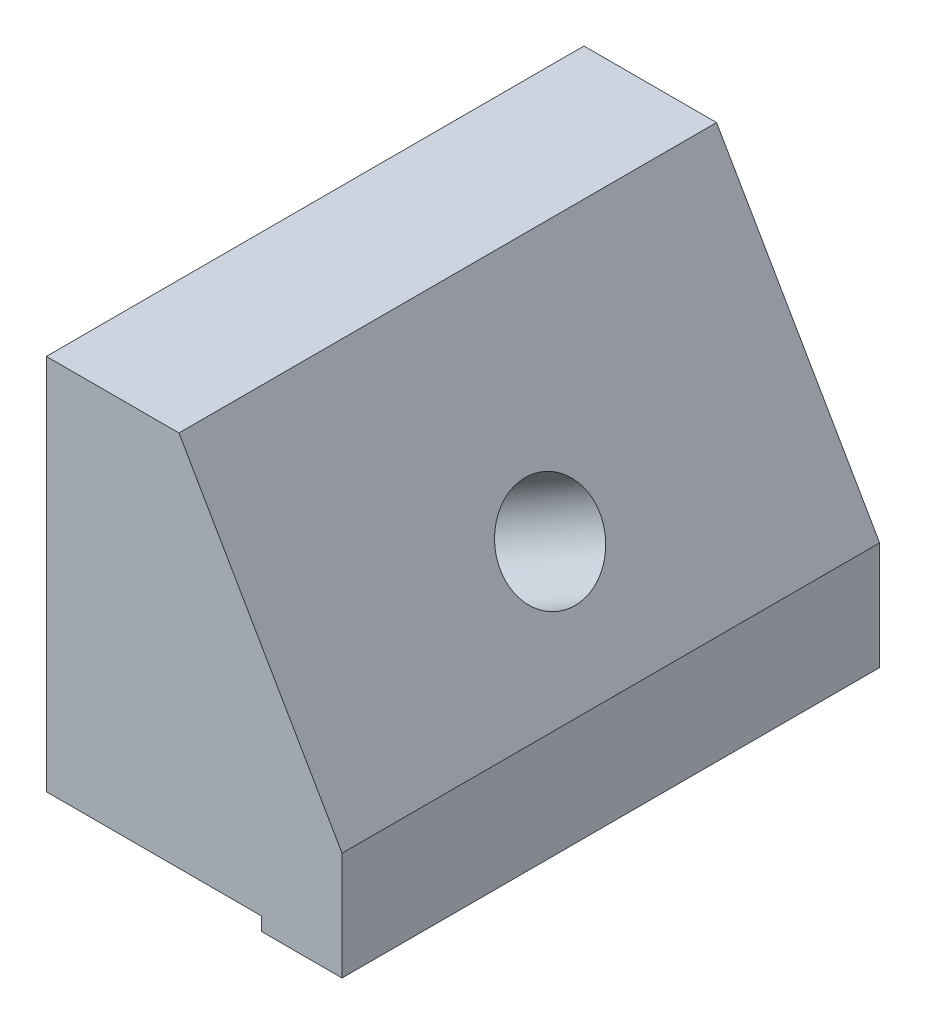
SolidWorks part; units mm, degrees
ref_plane "Спереди" through (0, 0, 0) normal (0, 0, 1) x (1, 0, 0)
ref_plane "Сверху" through (0, 0, 0) normal (0, 1, 0) x (1, 0, 0)
ref_plane "Справа" through (0, 0, 0) normal (1, 0, 0) x (0, 0, -1)
sketch "Эскиз1" plane through (0, 0, 0) normal (0, 0, 1) x (1, 0, 0)
  line L0 (-12.5, 21.6506) -> (0, 0)
  line L1 (0, 0) -> (12.9904, 7.5)
  line L2 (12.9904, 7.5) -> (0.4904, 29.1506)
  line L3 (0.4904, 29.1506) -> (-12.5, 21.6506)
extrude "Бобышка-Вытянуть1" add sketch "Эскиз1" along normal blind 20
sketch "Эскиз2" plane through (12.9904, 7.5, 0) normal (0.866, 0.5, 0) x (0, 0, -1)
  circle A0 centre (-10, 8) radius 1.85
extrude "Вырез-Вытянуть1" cut sketch "Эскиз2" against normal blind 6
sketch "Эскиз3" plane through (7.7942, 4.5, 0) normal (0.866, 0.5, 0) x (0, 0, -1)
  circle A0 centre (-10, 8) radius 1.125
extrude "Вырез-Вытянуть2" cut sketch "Эскиз3" against normal through all
sketch "Эскиз4" plane through (0, 0, 20) normal (0, 0, 1) x (1, 0, 0)
  line L0 (-12.5, 21.6506) -> (0, 0) construction
  line L1 (-3.75, 6.4952) -> (11.25, 6.4952)
  line L2 (-3.75, 6.4952) -> (-3.75, 26.7024)
  line L4 (11.25, 6.4952) -> (11.25, 10.5144)
  line L5 (0, 0) -> (12.9904, 7.5) construction
  line L6 (12.9904, 7.5) -> (0.4904, 29.1506) construction
  line L7 (0.4904, 29.1506) -> (-12.5, 21.6506) construction
  line L8 (-3.75, 26.7024) -> (1.9038, 26.7024)
  line L9 (1.9038, 26.7024) -> (11.25, 10.5144)
  point P6 (15.1592, 13.7435)
  point P7 (0, 0)
  point P10 (10.5535, 11.7208)
extrude "Вырез-Вытянуть3" cut sketch "Эскиз4" against normal through all flip side to cut
sketch "Эскиз5" plane through (0, 0, 20) normal (0, 0, 1) x (1, 0, 0)
  line L0 (1.9038, 26.7024) -> (-3.75, 26.7024) construction
  line L1 (0.25, 26.7024) -> (-3.75, 26.7024)
  line L2 (0.25, 26.7024) -> (0.25, 11.7024)
  line L3 (0.25, 11.7024) -> (-3.75, 11.7024)
  line L4 (-3.75, 26.7024) -> (-3.75, 11.7024)
  line L5 (-3.75, 26.7024) -> (-3.75, 6.4952) construction
  line L6 (-3.75, 6.4952) -> (11.25, 6.4952) construction
  line L7 (-3.75, 7.3952) -> (0.25, 7.3952)
  line L8 (-3.75, 7.3952) -> (-3.75, 6.4952)
  line L9 (-3.75, 6.4952) -> (0.25, 6.4952)
  line L10 (0.25, 7.3952) -> (0.25, 6.4952)
extrude "Вырез-Вытянуть4" cut sketch "Эскиз5" against normal through all
sketch "Эскиз6" plane through (0, 11.7024, 0) normal (0, 1, 0) x (1, 0, 0)
  line L5 (-3.75, 0) -> (-3.75, -20) construction
  line L11 (-3.75, -13) -> (0.25, -13)
  line L12 (-3.75, -13) -> (-3.75, -20)
  line L13 (-3.75, -20) -> (0.25, -20)
  line L14 (0.25, -13) -> (0.25, -20)
  line L15 (-3.75, -10) -> (11.25, -10) construction
  line L16 (11.25, 0) -> (11.25, -20) construction
  line L17 (0.25, -7) -> (0.25, 0)
  line L18 (-3.75, 0) -> (0.25, 0)
  line L19 (-3.75, -7) -> (-3.75, 0)
  line L20 (-3.75, -7) -> (0.25, -7)
extrude "Вырез-Вытянуть5" cut sketch "Эскиз6" against normal through all
sketch "Эскиз7" plane through (0, 0, 20) normal (0, 0, 1) x (1, 0, 0)
  line L0 (0.25, 21.0225) -> (5.1832, 21.0225)
  line L1 (0.25, 6.4952) -> (8.25, 6.4952)
  line L2 (0.25, 6.4952) -> (0.25, 6.9952)
  line L3 (0.25, 6.9952) -> (8.25, 6.9952)
  line L4 (8.25, 6.4952) -> (8.25, 6.9952)
  line L5 (0.25, 6.4952) -> (0.25, 26.7024) construction
  line L6 (11.25, 10.5144) -> (1.9038, 26.7024) construction
  line L8 (0.25, 26.7024) -> (0.25, 21.0225)
  line L9 (1.9038, 26.7024) -> (0.25, 26.7024) construction
  line L10 (0.25, 26.7024) -> (1.9038, 26.7024)
  line L11 (1.9038, 26.7024) -> (5.1832, 21.0225)
extrude "Вырез-Вытянуть6" cut sketch "Эскиз7" against normal through all
sketch "Эскиз8" plane through (0, 6.9952, 0) normal (0, -1, 0) x (1, 0, 0)
  line L0 (-3.75, 11.506) -> (0.25, 11.506)
  line L1 (-3.75, 11.0897) -> (-3.75, 13) construction
  line L2 (0.25, 0) -> (0.25, 20) construction
  line L3 (-3.75, 11.506) -> (-3.75, 8.494)
  line L4 (-3.75, 7) -> (-3.75, 8.9103) construction
  line L5 (-3.75, 8.494) -> (0.25, 8.494)
  line L6 (0.25, 7) -> (0.25, 13) construction
  arc A0 (0.25, 11.506) -> (0.25, 8.494) centre (0.25, 10) cw
  point P14 (0, 0)
extrude "Вырез-Вытянуть7" cut sketch "Эскиз8" against normal blind 2
